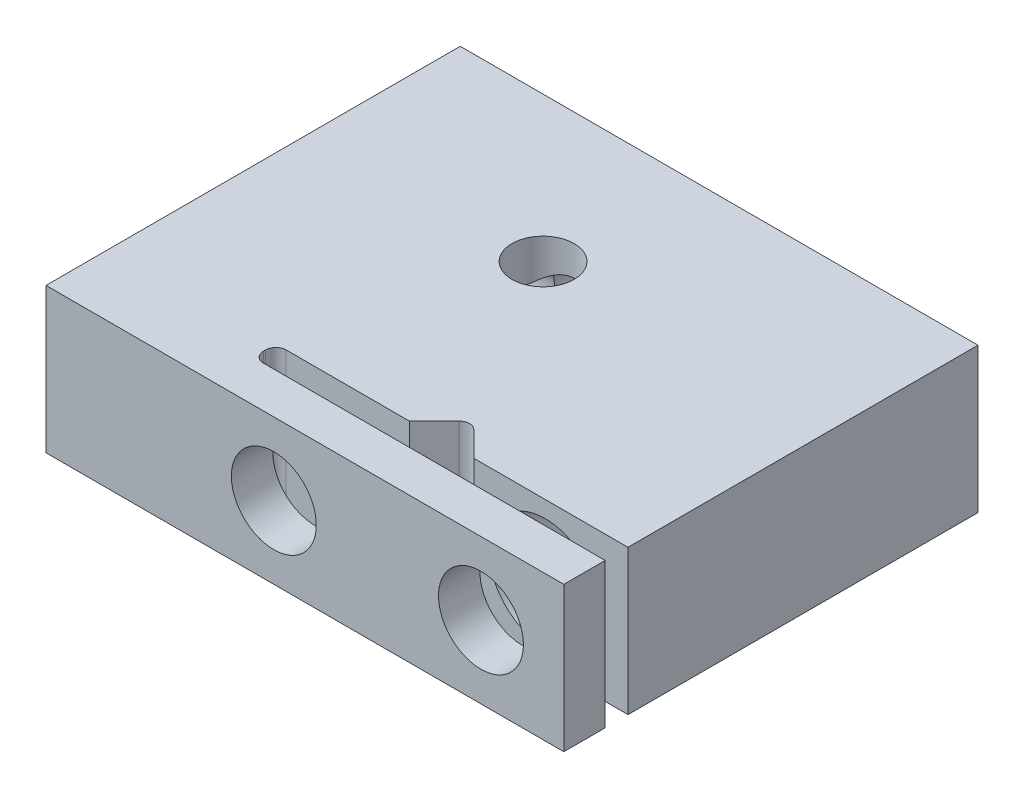
SolidWorks part; units mm, degrees
material "AISI 316 Annealed Stainless Steel Bar (SS)"
ref_plane "Front Plane" through (0, 0, 0) normal (0, 0, 1) x (1, 0, 0)
ref_plane "Top Plane" through (0, 0, 0) normal (0, 1, 0) x (1, 0, 0)
ref_plane "Right Plane" through (0, 0, 0) normal (1, 0, 0) x (0, 0, -1)
sketch "Sketch1" plane through (0, 0, 0) normal (0, 1, 0) x (1, 0, 0)
  line L1 (-6.25, 5) -> (6.25, 5)
  line L2 (-6.25, 5) -> (-6.25, -5)
  line L3 (-6.25, -5) -> (6.25, -5)
  line L4 (6.25, 5) -> (6.25, -5)
  point P4 (6.25, 0)
  point P6 (0, 5)
  dimension "D1" = 12.5
  dimension "D2" = 10
extrude "Boss-Extrude1" add sketch "Sketch1" along normal blind 3.5
sketch "Sketch2" plane through (0, 3.5, 0) normal (0, 1, 0) x (1, 0, 0)
  line L0 (1.75, -4) -> (6.25, -4)
  line L1 (6.25, -5) -> (6.25, 5) construction
  line L2 (6.25, -4) -> (6.25, -3.45)
  line L3 (6.25, -3.45) -> (2.5278, -3.45)
  line L4 (-6.25, -5) -> (6.25, -5) construction
  line L5 (1.75, -4) -> (-2, -4)
  line L6 (-2.25, -3.75) -> (-2.25, -3.7)
  line L7 (-2, -3.45) -> (0.9722, -3.45)
  line L8 (2.5278, -3.45) -> (1.9268, -2.849)
  line L9 (1.5732, -2.849) -> (0.9722, -3.45)
  circle A0 centre (1.75, -3.45) radius 0.55
  arc A1 (-2.25, -3.7) -> (-2, -3.45) centre (-2, -3.7) cw
  arc A2 (-2, -4) -> (-2.25, -3.75) centre (-2, -3.75) cw
  arc A3 (1.9268, -2.849) -> (1.5732, -2.849) centre (1.75, -3.0257) ccw
  point P6 (4, -4)
  point P22 (1.75, -2.6722)
  line M4 (6.25, -5) -> (6.25, 5)
  dimension "D1" = 1.1
  dimension "D5" = 0.25
  dimension "D6" = 0.25
  dimension "D2" = 1
  dimension "D3" = 4.5
  dimension "D4" = 8.5
extrude "Cut-Extrude1" cut sketch "Sketch2" against normal blind 3.5 contours A0 L0 L3 M4 | A0 | A0 L7 L6 L5 | L8 A3 L9 A0
hole_wizard "M2.5 Clearance Hole1" positions "Sketch3" profile "Sketch5" hole size "M2.5" standard "ISO" end condition up to next
sketch "Sketch3" plane through (0, 0, -5) normal (0, 0, -1) x (-1, 0, 0)
  line L1 (-6.25, 3.5) -> (-6.25, 0) construction
  line L2 (-6.25, 3.5) -> (-6.25, 0)
  point P0 (-4.25, 1.75)
  point P7 (-6.25, 1.75)
  dimension "D1" = 2
sketch "Sketch5" plane through (4.25, 1.75, -5) normal (1, 0, 0) x (0, 1, 0)
  line L0 (0, 0) -> (0, 8.45)
  line L1 (0, 8.45) -> (1.35, 8.45)
  line L2 (1.35, 8.45) -> (1.35, 0)
  line L5 (1.35, 0) -> (0, 0)
  line L11 (0, -6.35) -> (0, 107.95) construction
  dimension "Thru Hole Dia." = 2.7
  dimension "Thru Hole Depth" = 8.45
hole_wizard "M2.5 Tapped Hole1" positions "Sketch6" profile "Sketch7" tap size "M2.5" standard "ISO" end condition up to next
sketch "Sketch6" plane through (0, 0, 5) normal (0, 0, 1) x (1, 0, 0)
  circle A0 centre (4.25, 1.75) radius 1.35 construction
  circle A1 centre (4.25, 1.75) radius 1.35
  point P0 (4.25, 1.75)
sketch "Sketch7" plane through (4.25, 1.75, 5) normal (1, 0, 0) x (0, -1, 0)
  line L0 (0, 0) -> (0, 1)
  line L1 (0, 1) -> (1.025, 1)
  line L2 (1.025, 1) -> (1.025, 0)
  line L5 (1.025, 0) -> (0, 0)
  line L11 (0, -6.35) -> (0, 107.95) construction
  dimension "Thru Tap Drill Dia." = 2.05
  dimension "Thru Tap Drill Depth" = 1
cosmetic thread "Hole Thread1" parameters "D2"=2.5
hole_wizard "Ø1.5 (1.5) Diameter Hole1" positions "Sketch8" profile "Sketch9" hole size "Ø1.5" standard "ISO" end condition up to next
sketch "Sketch8" plane through (0, 3.5, 0) normal (0, 1, 0) x (1, 0, 0)
  line L0 (6.25, -3.45) -> (6.25, 5) construction
  line L1 (6.25, 5) -> (-6.25, 5) construction
  point P0 (-0.75, 1.5)
  dimension "D1" = 7
  dimension "D2" = 3.5
sketch "Sketch9" plane through (-0.75, 3.5, -1.5) normal (1, 0, 0) x (0, 0, 1)
  line L0 (0, 0) -> (0, 3.5)
  line L1 (0, 3.5) -> (0.75, 3.5)
  line L2 (0.75, 3.5) -> (0.75, 0)
  line L5 (0.75, 0) -> (0, 0)
  line L11 (0, -6.35) -> (0, 107.95) construction
  dimension "Thru Hole Dia." = 1.5
  dimension "Thru Hole Depth" = 3.5
hole_wizard "M2.5 Tapped Hole2" positions "Sketch10" profile "Sketch11" tap size "M2.5" standard "ISO" end condition through all
sketch "Sketch10" plane through (0, 0, -5) normal (0, 0, -1) x (-1, 0, 0)
  line L0 (-6.25, 3.5) -> (-6.25, 0) construction
  line L1 (-6.25, 3.5) -> (-6.25, 0)
  point P0 (0.75, 1.75)
  point P5 (-6.25, 1.75)
  dimension "D1" = 7
sketch "Sketch11" plane through (-0.75, 1.75, -5) normal (1, 0, 0) x (0, 1, 0)
  line L0 (0, 0) -> (0, 10)
  line L1 (0, 10) -> (1.025, 10)
  line L2 (1.025, 10) -> (1.025, 0)
  line L5 (1.025, 0) -> (0, 0)
  line L11 (0, -6.35) -> (0, 107.95) construction
  dimension "Thru Tap Drill Dia." = 2.05
  dimension "Thru Tap Drill Depth" = 10
cosmetic thread "Hole Thread2" parameters "D2"=2.5
hole_wizard "M2 Tapped Hole3" positions "Sketch13" profile "Sketch14" tap size "M2" standard "ISO"
sketch "Sketch13" plane through (-6.25, 0, 0) normal (-1, 0, 0) x (0, 0, 1)
  line L0 (-5, 3.5) -> (-5, 0) construction
  line L1 (-5, 3.5) -> (-5, 0)
  line L2 (5, 3.5) -> (5, 0) construction
  point P0 (-2, 1.75)
  point P2 (2.5, 1.75)
  point P7 (-5, 1.75)
  dimension "D1" = 2.5
  dimension "D2" = 4.5
sketch "Sketch14" plane through (-6.25, 1.75, -2) normal (0, 1, 0) x (0, 0, 1)
  line L0 (0, 0) -> (0, 5.4807)
  line L1 (0, 5.4807) -> (0.8, 5)
  line L2 (0.8, 5) -> (0.8, 0)
  line L5 (0.8, 0) -> (0, 0)
  line L10 (0, 5.4807) -> (-0.8, 5) construction
  line L11 (0, -6.35) -> (0, 107.95) construction
  dimension "Tap Drill Dia." = 1.6
  dimension "Tap Drill Depth" = 5
  dimension "Drill Angle" = 118
cosmetic thread "Hole Thread5" parameters "D1"=4, "D2"=2
cosmetic thread "Hole Thread6" parameters "D1"=4, "D2"=2
hole_wizard "M2 Tapped Hole1" [suppressed] positions "Sketch17" profile "Sketch18" tap size "M2" standard "ISO"
sketch "Sketch17" plane through (0, 0, 0) normal (0, -1, 0) x (-1, 0, 0)
  line L0 (6, -5) -> (-6, -5) construction
  arc A0 (-1.8232, -2.849) -> (-2.1768, -2.849) centre (-2, -3.0257) ccw construction
  arc A1 (-1.8232, -2.849) -> (-2.1768, -2.849) centre (-2, -3.0257) ccw
  point P0 (-2, 0)
  dimension "D1" = 5
sketch "Sketch18" plane through (2, 0, 0) normal (1, 0, 0) x (0, 0, -1)
  line L0 (0, 0) -> (0, 3.5)
  line L1 (0, 3.5) -> (0.8, 3.5)
  line L2 (0.8, 3.5) -> (0.8, 0)
  line L5 (0.8, 0) -> (0, 0)
  line L11 (0, -6.35) -> (0, 107.95) construction
  dimension "Thru Tap Drill Dia." = 1.6
  dimension "Thru Tap Drill Depth" = 3.5
cosmetic thread "Hole Thread8" [suppressed] parameters "D2"=2
